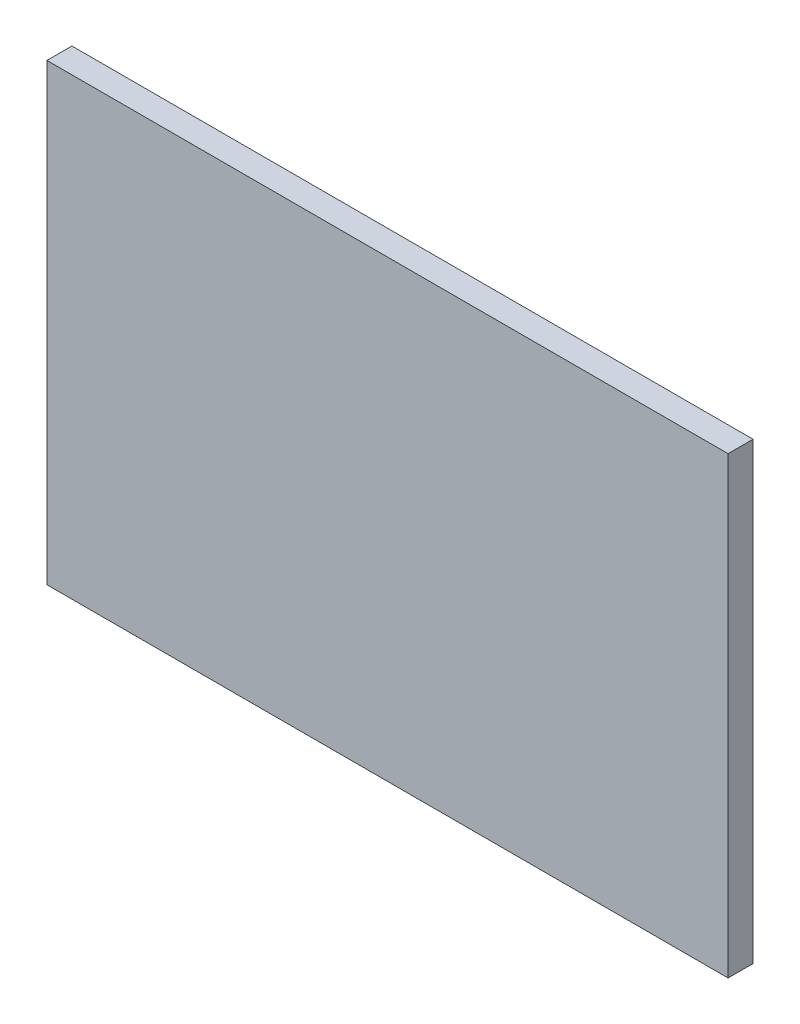
SolidWorks part; units mm, degrees
ref_plane "前视基准面" through (0, 0, 0) normal (0, 0, 1) x (1, 0, 0)
ref_plane "上视基准面" through (0, 0, 0) normal (0, 1, 0) x (1, 0, 0)
ref_plane "右视基准面" through (0, 0, 0) normal (1, 0, 0) x (0, 0, -1)
sketch "草图1" plane through (0, 0, 0) normal (0, 0, 1) x (1, 0, 0)
  line L1 (-11.7513, 12.3094) -> (18.2487, 12.3094)
  line L2 (-11.7513, 12.3094) -> (-11.7513, -7.6906)
  line L3 (-11.7513, -7.6906) -> (18.2487, -7.6906)
  line L4 (18.2487, 12.3094) -> (18.2487, -7.6906)
  circle A0 centre (0, 0) radius 6.25 construction
  dimension "D1" = 12.5
  dimension "D2" = 20
  dimension "D3" = 30
extrude "凸台-拉伸1" add sketch "草图1" along normal blind 1.1
